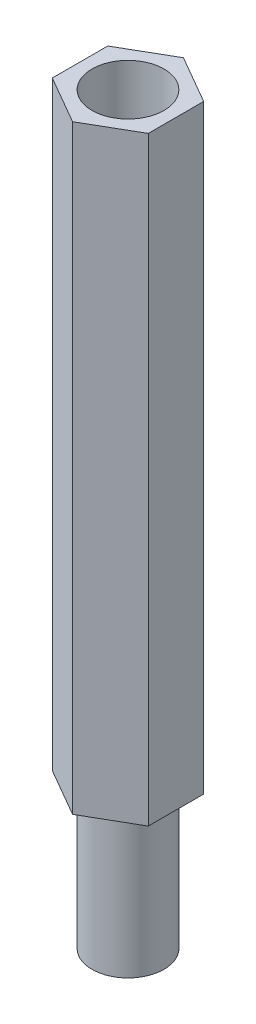
SolidWorks part; units mm, degrees
material "Brass"
ref_plane "Front Plane" through (0, 0, 0) normal (0, 0, 1) x (1, 0, 0)
ref_plane "Top Plane" through (0, 0, 0) normal (0, 1, 0) x (1, 0, 0)
ref_plane "Right Plane" through (0, 0, 0) normal (1, 0, 0) x (0, 0, -1)
sketch "Sketch1" plane through (0, 0, 0) normal (0, 1, 0) x (1, 0, 0)
  line L1 (0, -2.3094) -> (2, -1.1547)
  line L2 (2, -1.1547) -> (2, 1.1547)
  line L3 (2, 1.1547) -> (0, 2.3094)
  line L4 (0, 2.3094) -> (-2, 1.1547)
  line L5 (-2, 1.1547) -> (-2, -1.1547)
  line L6 (-2, -1.1547) -> (0, -2.3094)
  circle A1 centre (0, 0) radius 2 construction
  circle A2 centre (0, 0) radius 2.3094 construction
  dimension "D2" = 4
extrude "Boss-Extrude1" add sketch "Sketch1" along normal blind 25
sketch "Sketch2" plane through (0, 25, 0) normal (0, 1, 0) x (1, 0, 0)
  circle A0 centre (0, 0) radius 1.5
  dimension "D1" = 3
extrude "Cut-Extrude1" cut sketch "Sketch2" against normal blind 19
sketch "Sketch3" plane through (0, 0, 0) normal (0, -1, 0) x (1, 0, 0)
  circle A0 centre (0, 0) radius 1.5
  dimension "D1" = 3
extrude "Boss-Extrude2" add sketch "Sketch3" along normal blind 6
